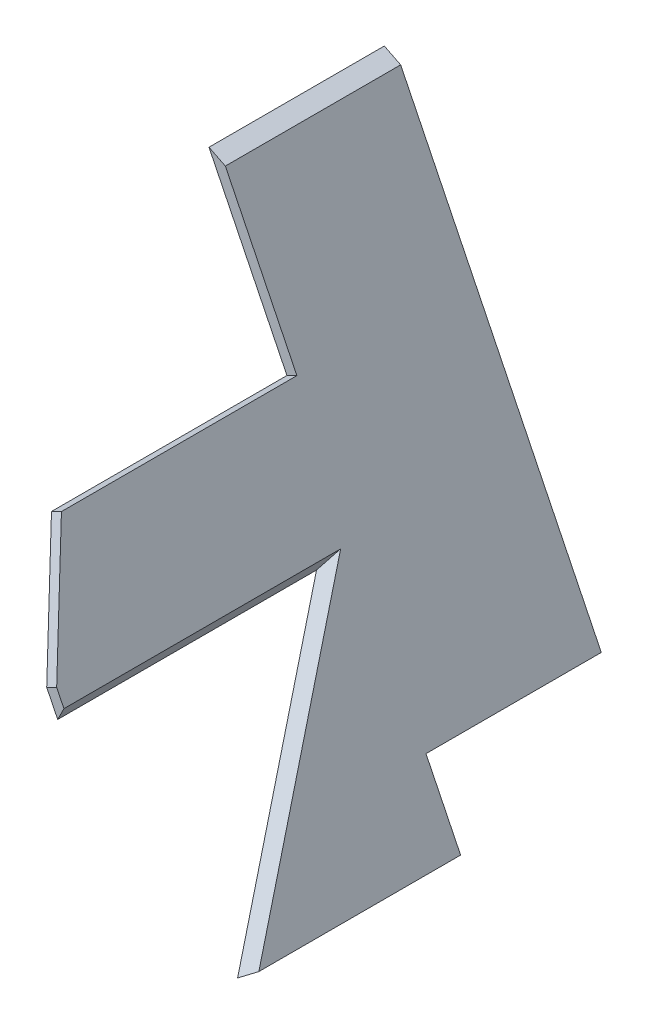
SolidWorks part; units mm, degrees
ref_plane "Front Plane" through (0, 0, 0) normal (0, 0, 1) x (1, 0, 0)
ref_plane "Top Plane" through (0, 0, 0) normal (0, 1, 0) x (1, 0, 0)
ref_plane "Right Plane" through (0, 0, 0) normal (1, 0, 0) x (0, 0, -1)
sketch "Sketch2" plane through (0, 0, 133.3236) normal (0, 0, 1) x (1, 0, 0)
  line L8 (-510.3993, 217.586) -> (-679.2205, 561.3714) construction
  line L9 (-552.0963, 302.4973) -> (-547.6083, 304.7012)
  line L10 (-552.0963, 302.4973) -> (-662.2599, 526.8329)
  line L11 (-547.6083, 304.7012) -> (-659.457, 532.4685)
  line L12 (-662.2599, 526.8329) -> (-659.457, 532.4685)
  line L13 (-505.9112, 219.7899) -> (-674.7325, 563.5753) construction
  line L15 (-718.8004, 413.1495) -> (-789.3595, 271.2798) construction
extrude "Boss-Extrude1" add sketch "Sketch2" along normal up to surface (208.2958 mm away)
sketch "Sketch3" plane through (56.4565, 113.5145, 99.0505) normal (-0.3509, -0.7056, -0.6157) x (-0.9357, 0.2396, 0.2588)
  line L0 (641.8774, 324.8914) -> (520.568, 262.7181)
  line L1 (641.8774, 324.8914) -> (811.3852, -162.5711)
  line L2 (520.568, 262.7181) -> (690.0758, -224.7444)
  line L3 (811.3852, -162.5711) -> (690.0758, -224.7444)
  line L4 (655.2821, -124.6865) -> (601.3716, 30.347) construction
  line L5 (640.5133, 328.8143) -> (709.4467, 130.5786) construction
extrude "Cut-Extrude1" cut sketch "Sketch3" against normal through all
sketch "Sketch5" plane through (-325.1433, -159.6668, 0) normal (-0.8976, -0.4408, 0) x (0, 0, 1)
  line L0 (263.8236, 620.5449) -> (263.8236, 631.782)
  line L1 (147.1849, 620.5449) -> (341.6195, 620.5449) construction
  line L2 (263.8236, 553.6542) -> (263.8236, 615.3521) construction
  line L3 (263.8236, 631.782) -> (239.4303, 682.2494)
  line L4 (239.4303, 682.2494) -> (133.3236, 682.2494)
  line L5 (133.3236, 764.8068) -> (133.3236, 514.8818) construction
  line L6 (133.3236, 682.2494) -> (133.3236, 768.6299)
  line L8 (133.3236, 768.6299) -> (341.6195, 768.6299)
  line L9 (341.6195, 768.6299) -> (341.6195, 620.5449)
  line L10 (341.6195, 764.8068) -> (341.6195, 620.5449) construction
  line L11 (341.6195, 620.5449) -> (263.8236, 620.5449)
  line L12 (341.6195, 768.6299) -> (133.3236, 768.6299) construction
extrude "Cut-Extrude3" cut sketch "Sketch5" against normal through all
sketch "Sketch6" plane through (0, 0, 133.3236) normal (0, 0, -1) x (-1, 0, 0)
  line L0 (567.7015, 334.2755) -> (563.2135, 336.4795)
  line L1 (567.7015, 334.2755) -> (660.9969, 524.261)
  line L2 (563.2135, 336.4795) -> (653.6265, 520.5953)
  line L3 (660.9969, 524.261) -> (653.6265, 520.5953)
  line L6 (625.8697, 452.7284) -> (552.0963, 302.4973) construction
  line L7 (547.6083, 304.7012) -> (621.3816, 454.9324) construction
  line L8 (567.7015, 334.2755) -> (679.903, 279.1772) construction
  line L11 (663.0349, 525.2746) -> (439.5496, 414.1239) construction
extrude "Boss-Extrude2" add sketch "Sketch6" along normal up to surface (79 mm away)
